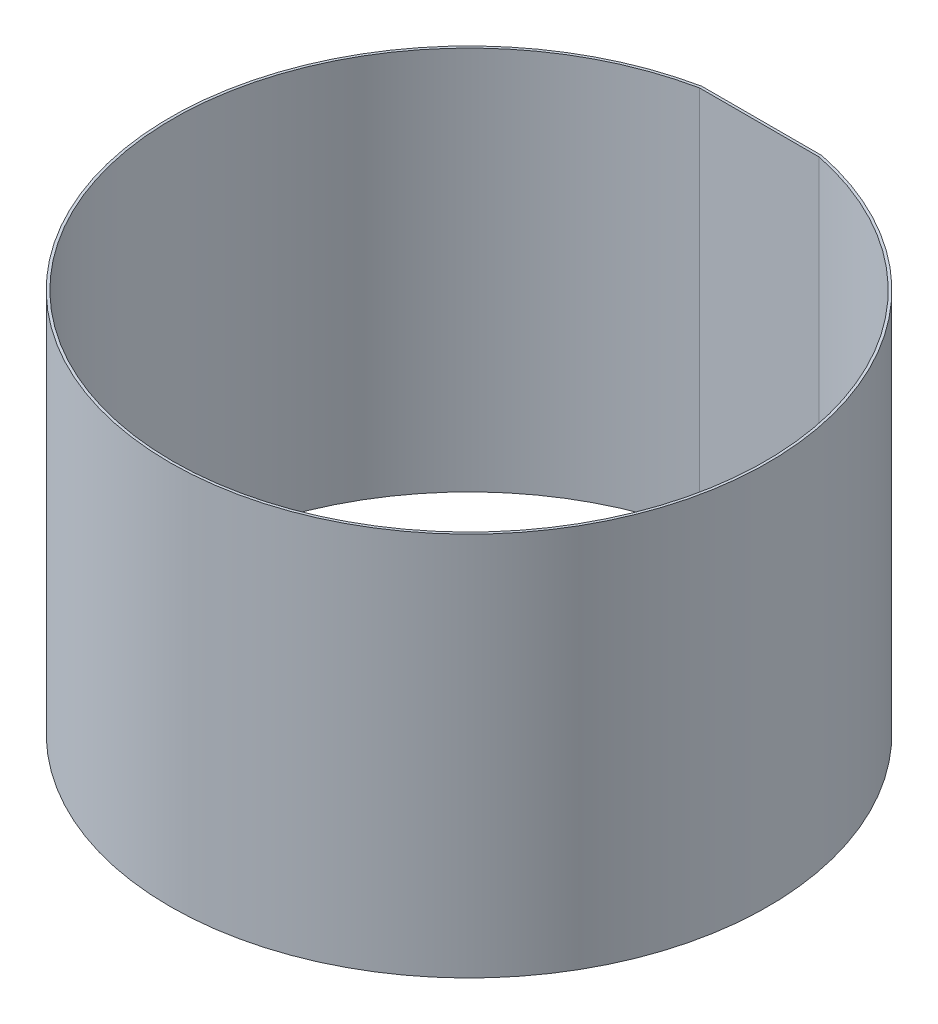
SolidWorks part; units mm, degrees
material "AISI 316 Stainless Steel Sheet (SS)"
ref_plane "Front Plane" through (0, 0, 0) normal (0, 0, 1) x (1, 0, 0)
ref_plane "Top Plane" through (0, 0, 0) normal (0, 1, 0) x (1, 0, 0)
ref_plane "Right Plane" through (0, 0, 0) normal (1, 0, 0) x (0, 0, -1)
sketch "Sketch1" plane through (0, 0, 0) normal (0, 1, 0) x (1, 0, 0)
  line L0 (-35, 169.9331) -> (35, 169.9331)
  line L1 (0, 169.9331) -> (0, 0) construction
  line L8 (-155, 37.5278) -> (-110, 115.4701)
  line L9 (-110, 115.4701) -> (-58.5, 90)
  line L10 (-58.5, 90) -> (58.5, 90)
  line L17 (-132.5, 76.4989) -> (0, 0) construction
  line L18 (110, 115.4701) -> (58.5, 90)
  line L19 (155, 37.5278) -> (110, 115.4701)
  line L20 (-155, 37.5278) -> (-107.1923, 5.6625)
  line L21 (-107.1923, 5.6625) -> (-48.6923, -95.6625)
  line L22 (-35.1525, 171.4331) -> (35.1525, 171.4331)
  circle A0 centre (0, 0) radius 170 construction
  arc A2 (-35, 169.9331) -> (35, 169.9331) centre (0, 0) ccw
  arc A39 (-35.1525, 171.4331) -> (35.1525, 171.4331) centre (0, 0) ccw
  point P58 (0, 90)
  dimension "D1" = 340
  dimension "D2" = 155
  dimension "D8" = 3.5
  dimension "D3" = 90
  dimension "D4" = 60
  dimension "D5" = 90
  dimension "D6" = 58.5
  dimension "D7" = 70
  dimension "D9" = 1.5
extrude "Boss-Extrude1" add sketch "Sketch1" along normal blind 225 contours L22 A39 A2 L0
